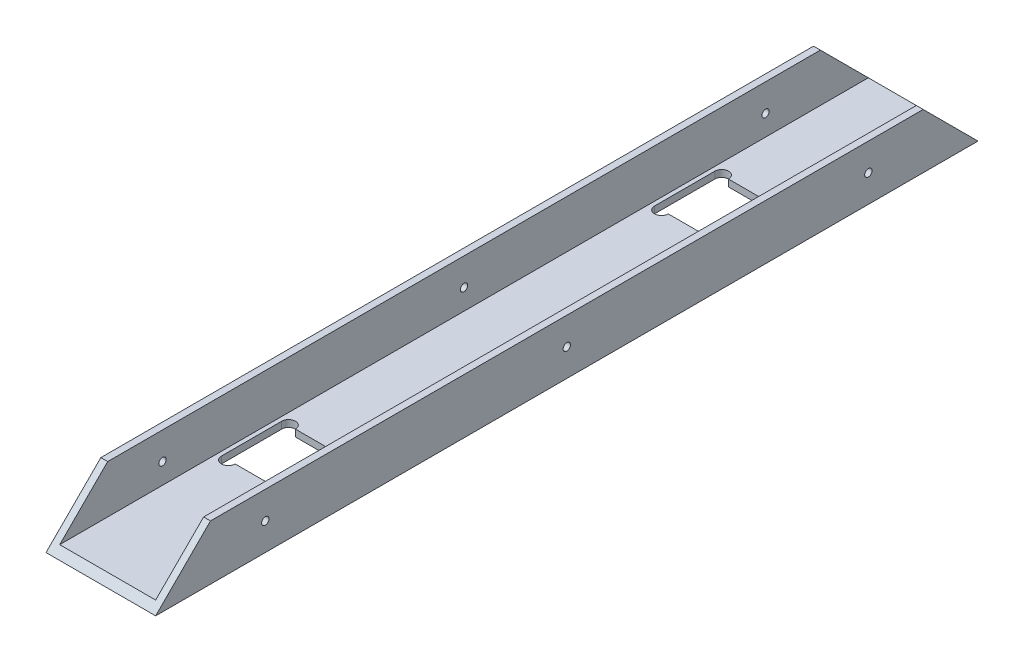
SolidWorks part; units mm, degrees
material "6061 Alloy"
ref_plane "Front Plane" through (0, 0, 0) normal (0, 0, 1) x (1, 0, 0)
ref_plane "Top Plane" through (0, 0, 0) normal (0, 1, 0) x (1, 0, 0)
ref_plane "Right Plane" through (0, 0, 0) normal (1, 0, 0) x (0, 0, -1)
sketch "Sketch1" plane through (0, 0, 0) normal (0, 0, 1) x (1, 0, 0)
  line L0 (-25.4, 0) -> (25.4, 0)
  line L1 (25.4, 0) -> (25.4, 25.4)
  line L2 (25.4, 25.4) -> (22.225, 25.4)
  line L3 (22.225, 25.4) -> (22.225, 3.175)
  line L4 (22.225, 3.175) -> (-22.225, 3.175)
  line L5 (-22.225, 3.175) -> (-22.225, 25.4)
  line L6 (-22.225, 25.4) -> (-25.4, 25.4)
  line L7 (-25.4, 25.4) -> (-25.4, 0)
  line L8 (0, 15.5567) -> (0, -9.8218) construction
  dimension "D1" = 3.175
  dimension "D2" = 3.175
  dimension "D3" = 25.4
  dimension "D4" = 50.8
extrude "Boss-Extrude1" add sketch "Sketch1" along normal blind 381
sketch "Sketch2" plane through (25.4, 0, 0) normal (1, 0, 0) x (0, 0, -1)
  line L0 (-381, 0) -> (-355.6, 25.4)
  line L1 (-381, 25.4) -> (0, 25.4) construction
  line L2 (-355.6, 25.4) -> (-381, 25.4)
  line L3 (-381, 25.4) -> (-381, 0)
  line L4 (0, 0) -> (0, 25.4)
  line L5 (0, 25.4) -> (-25.4, 25.4)
  line L6 (-25.4, 25.4) -> (0, 0)
  dimension "D1" = 45
  dimension "D2" = 45
extrude "Cut-Extrude1" cut sketch "Sketch2" against normal through all
sketch "Sketch3" [suppressed] plane through (0, 0, 0) normal (0, -1, 0) x (1, 0, 0)
  line L0 (0, 304.8) -> (0, 0) construction
  line L1 (-25.4, 304.8) -> (25.4, 304.8) construction
  line L2 (-25.4, 0) -> (25.4, 0) construction
  circle A0 centre (0, 254) radius 2.5
  circle A1 centre (0, 76.2) radius 2.5
  dimension "D3" = 19.05
  dimension "D1" = 177.8
  dimension "D2" = 76.2
extrude "Cut-Extrude2" [suppressed] cut sketch "Sketch3" against normal blind 330.2
sketch "Sketch4" plane through (0, 0, 0) normal (0, -1, 0) x (1, 0, 0)
  line L0 (0, 381) -> (0, 0) construction
  line L1 (-25.4, 381) -> (25.4, 381) construction
  line L2 (-25.4, 190.5) -> (25.4, 190.5) construction
  line L3 (-13.97, 276.86) -> (13.97, 276.86)
  line L4 (-20.32, 276.86) -> (-20.32, 304.8)
  line L5 (-13.97, 304.8) -> (13.97, 304.8)
  line L6 (20.32, 276.86) -> (20.32, 304.8)
  line L7 (-20.32, 276.86) -> (20.32, 304.8) construction
  line L8 (-20.32, 304.8) -> (20.32, 276.86) construction
  line L9 (-25.4, 381) -> (-25.4, 0) construction
  line L10 (25.4, 381) -> (25.4, 0) construction
  line L11 (-20.32, 104.14) -> (-20.32, 76.2)
  line L12 (-13.97, 104.14) -> (13.97, 104.14)
  line L17 (-25.4, 290.83) -> (25.4, 290.83) construction
  line L18 (20.32, 104.14) -> (20.32, 76.2)
  line L19 (-13.97, 76.2) -> (13.97, 76.2)
  arc A0 (-13.97, 304.8) -> (-20.32, 304.8) centre (-17.145, 304.8) ccw
  arc A1 (13.97, 304.8) -> (20.32, 304.8) centre (17.145, 304.8) cw
  arc A2 (13.97, 276.86) -> (20.32, 276.86) centre (17.145, 276.86) ccw
  arc A3 (-13.97, 276.86) -> (-20.32, 276.86) centre (-17.145, 276.86) cw
  arc A4 (-13.97, 76.2) -> (-20.32, 76.2) centre (-17.145, 76.2) cw
  arc A5 (-13.97, 104.14) -> (-20.32, 104.14) centre (-17.145, 104.14) ccw
  arc A6 (13.97, 104.14) -> (20.32, 104.14) centre (17.145, 104.14) cw
  arc A7 (13.97, 76.2) -> (20.32, 76.2) centre (17.145, 76.2) ccw
  point P5 (0, 290.83)
  dimension "D4" = 6.35
  dimension "D1" = 27.94
  dimension "D2" = 40.64
  dimension "D3" = 76.2
extrude "Cut-Extrude3" cut sketch "Sketch4" against normal through all
sketch "Sketch5" plane through (-25.4, 0, 0) normal (-1, 0, 0) x (0, 0, 1)
  line L0 (12.7, 12.7) -> (368.3, 12.7) construction
  line L1 (25.4, 25.4) -> (0, 0) construction
  line L2 (381, 0) -> (355.6, 25.4) construction
  line L3 (190.5, 12.7) -> (190.5, 25.4) construction
  line L4 (355.6, 25.4) -> (25.4, 25.4) construction
  line L5 (0, 0) -> (0, 25.4) construction
  point P10 (50.8, 12.7)
  point P11 (330.2, 12.7)
  dimension "D1" = 50.8
hole_wizard "M3 Clearance Hole1" positions "3DSketch1" profile "Sketch6" hole size "M3" standard "ANSI Metric" end condition through all
sketch3d "3DSketch1"
  point P0 (-25.4, 12.7, 50.8)
  point P3 (-25.4, 12.7, 190.5)
  point P6 (-25.4, 12.7, 330.2)
sketch "Sketch6" plane through (-25.4, 12.7, 50.8) normal (0, 1, 0) x (0, 0, 1)
  line L0 (0, 0) -> (0, 50.8)
  line L1 (0, 50.8) -> (1.7, 50.8)
  line L2 (1.7, 50.8) -> (1.7, 0)
  line L5 (1.7, 0) -> (0, 0)
  line L11 (0, -6.35) -> (0, 107.95) construction
  dimension "Thru Hole Dia." = 3.4
  dimension "Thru Hole Depth" = 50.8
equation "\"D2@Sketch1\"=\"D1@Sketch1\""
